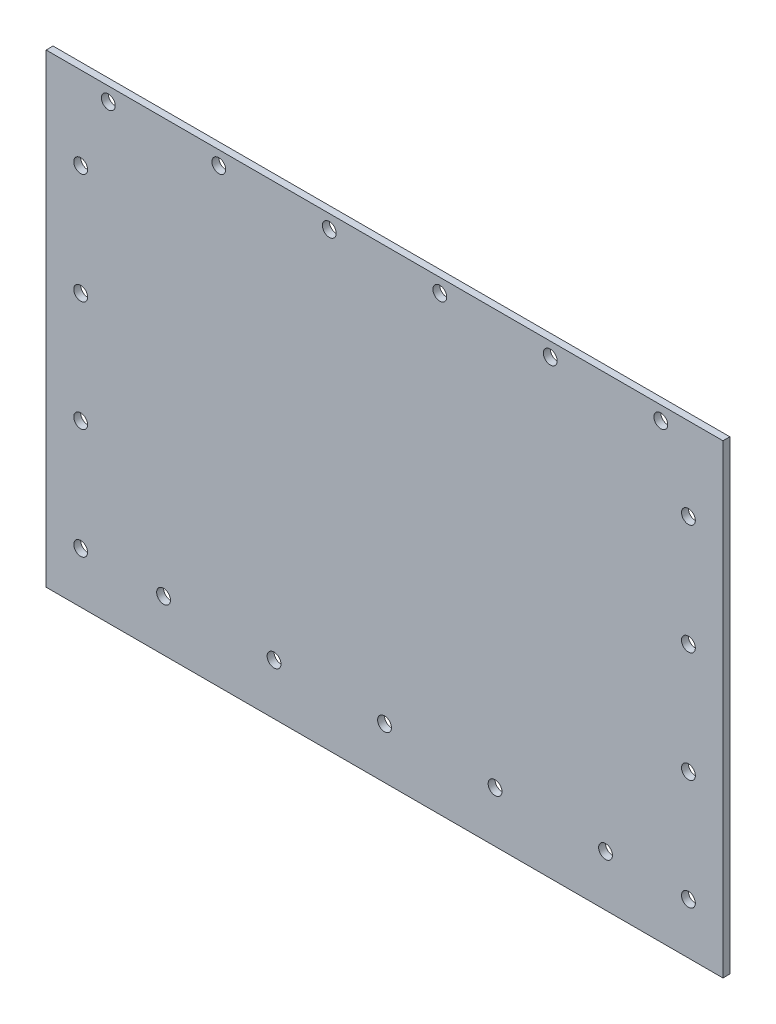
SolidWorks part; units mm, degrees
material "Copper"
ref_plane "Front Plane" through (0, 0, 0) normal (0, 0, 1) x (1, 0, 0)
ref_plane "Top Plane" through (0, 0, 0) normal (0, 1, 0) x (1, 0, 0)
ref_plane "Right Plane" through (0, 0, 0) normal (1, 0, 0) x (0, 0, -1)
sketch "Sketch2" plane through (0, 0, 0) normal (0, 0, 1) x (1, 0, 0)
  line L0 (0, -106.95) -> (155.58, -106.95)
  line L1 (0, 0) -> (155.58, 0)
  line L2 (0, 0) -> (0, -273.05)
  line L3 (0, -273.05) -> (155.58, -273.05)
  line L4 (155.58, 0) -> (155.58, -273.05)
  line L5 (0, -107.95) -> (155.58, -107.95)
  circle A0 centre (7.94, -19.05) radius 1.5875
  circle A1 centre (147.64, -19.05) radius 1.5875
  circle A2 centre (147.64, -44.45) radius 1.5875
  circle A3 centre (147.64, -69.85) radius 1.5875
  circle A4 centre (147.64, -95.25) radius 1.5875
  circle A5 centre (147.64, -120.65) radius 1.5875
  circle A6 centre (147.64, -146.05) radius 1.5875
  circle A7 centre (147.64, -171.45) radius 1.5875
  circle A8 centre (147.64, -196.85) radius 1.5875
  circle A9 centre (147.64, -222.25) radius 1.5875
  circle A10 centre (147.64, -247.65) radius 1.5875
  circle A11 centre (7.94, -44.45) radius 1.5875
  circle A12 centre (7.94, -69.85) radius 1.5875
  circle A13 centre (7.94, -95.25) radius 1.5875
  circle A14 centre (7.94, -120.65) radius 1.5875
  circle A15 centre (7.94, -146.05) radius 1.5875
  circle A16 centre (7.94, -171.45) radius 1.5875
  circle A17 centre (7.94, -196.85) radius 1.5875
  circle A18 centre (7.94, -222.25) radius 1.5875
  circle A19 centre (7.94, -247.65) radius 1.5875
  circle A20 centre (14.29, -3.175) radius 1.5875
  circle A21 centre (39.69, -3.175) radius 1.5875
  circle A22 centre (65.09, -3.175) radius 1.5875
  circle A23 centre (90.49, -3.175) radius 1.5875
  circle A24 centre (115.89, -3.175) radius 1.5875
  circle A25 centre (141.29, -3.175) radius 1.5875
  circle A26 centre (26.987, -266.7) radius 1.5875
  circle A27 centre (52.387, -266.7) radius 1.5875
  circle A28 centre (77.787, -266.7) radius 1.5875
  circle A29 centre (103.187, -266.7) radius 1.5875
  circle A30 centre (128.587, -266.7) radius 1.5875
  circle A31 centre (26.99, -95.25) radius 1.5875
  circle A32 centre (52.39, -95.25) radius 1.5875
  circle A33 centre (77.79, -95.25) radius 1.5875
  circle A34 centre (103.19, -95.25) radius 1.5875
  circle A35 centre (128.59, -95.25) radius 1.5875
  circle A36 centre (26.99, -120.65) radius 1.5875
  circle A37 centre (52.39, -120.65) radius 1.5875
  circle A38 centre (77.79, -120.65) radius 1.5875
  circle A39 centre (103.19, -120.65) radius 1.5875
  circle A40 centre (128.59, -120.65) radius 1.5875
  point P4 (0, 0)
  point P83 (23.467, -5.6571)
  dimension "D3" = 3.175
  dimension "D27" = 25.4
  dimension "D1" = 155.58
  dimension "D2" = 273.05
  dimension "D4" = 19.05
  dimension "D5" = 7.94
  dimension "D8" = 25.4
  dimension "D9" = 7.94
  dimension "D10" = 3.175
  dimension "D11" = 14.29
  dimension "D13" = 25.4
  dimension "D14" = 6.35
  dimension "D15" = 26.987
  dimension "D17" = 25.4
  dimension "D18" = 11.7
  dimension "D19" = 1
  dimension "D21" = 26.99
  dimension "D23" = 25.4
  dimension "D24" = 26.99
  dimension "D25" = 25.4
  dimension "D6" = 2
  dimension "D7" = 10
  dimension "D12" = 6
  dimension "D16" = 5
  dimension "D22" = 5
  dimension "D26" = 5
extrude "Boss-Extrude2" add sketch "Sketch2" along normal blind 1.5875 contours L4 L1 L2 L0 A35 A34 A33 A32 A31 A25 A24 A23 A22 A21 A20 A13 A12 A11 A4 A3 A2 A1 A0
